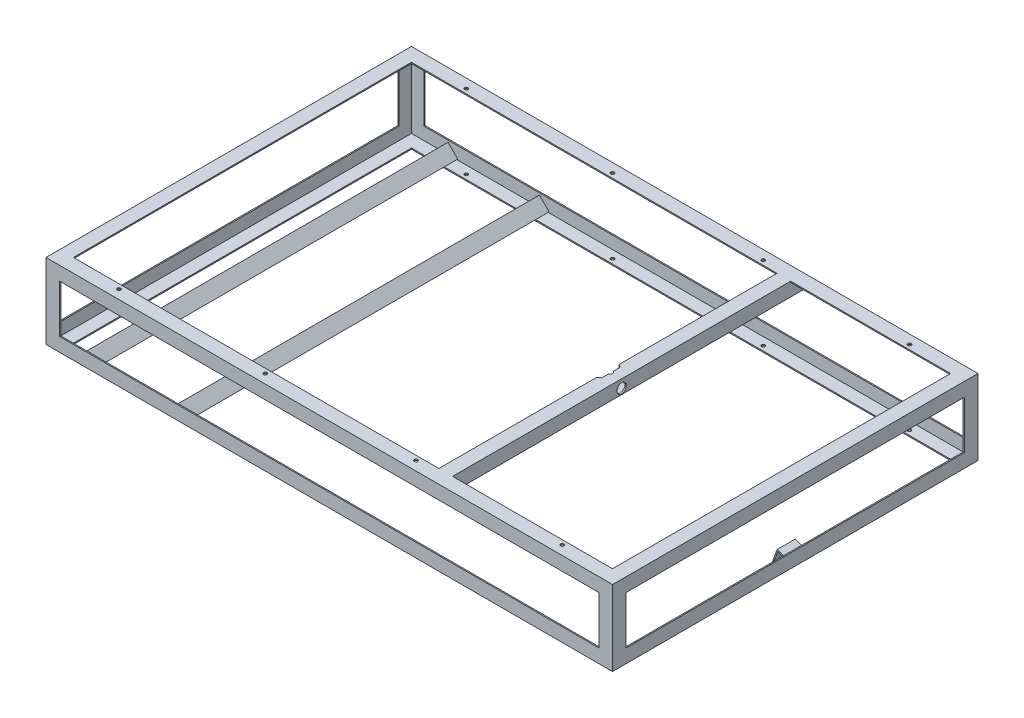
SolidWorks part; units mm, degrees
material "6061 Alloy"
ref_plane "Front Plane" through (0, 0, 0) normal (0, 0, 1) x (1, 0, 0)
ref_plane "Top Plane" through (0, 0, 0) normal (0, 1, 0) x (1, 0, 0)
ref_plane "Right Plane" through (0, 0, 0) normal (1, 0, 0) x (0, 0, -1)
other "Center of Mass"
sketch "Sketch2" plane through (0, 0, 0) normal (1, 0, 0) x (0, 0, -1)
  line L0 (-504.825, -346.075) -> (-504.825, -422.275)
  line L1 (504.825, -422.275) -> (-504.825, -422.275) construction
  line L2 (504.825, -422.275) -> (504.825, 422.275) construction
  line L3 (504.825, 422.275) -> (-504.825, 422.275) construction
  line L4 (-504.825, -422.275) -> (-504.825, 422.275) construction
  line L5 (504.825, -422.275) -> (-504.825, 422.275) construction
  line L6 (504.825, 422.275) -> (-504.825, -422.275) construction
  line L7 (-504.825, -422.275) -> (-428.625, -422.275)
  line L8 (-428.625, -422.275) -> (-428.625, -417.195)
  line L9 (-428.625, -417.195) -> (-498.7519, -417.195)
  line L10 (-498.7519, -417.195) -> (-498.7519, -346.075)
  line L11 (-498.7519, -346.075) -> (-504.825, -346.075)
  line L12 (0, 0) -> (0, -148.4726) construction
  line L13 (0, 0) -> (158.633, 0) construction
  line L14 (498.7519, -417.195) -> (498.7519, -346.075)
  line L15 (428.625, -417.195) -> (498.7519, -417.195)
  line L16 (428.625, -422.275) -> (428.625, -417.195)
  line L17 (504.825, -422.275) -> (428.625, -422.275)
  line L18 (504.825, -346.075) -> (504.825, -422.275)
  line L19 (498.7519, -346.075) -> (504.825, -346.075)
  line L20 (428.625, 417.195) -> (498.7519, 417.195)
  line L21 (428.625, 422.275) -> (428.625, 417.195)
  line L22 (504.825, 422.275) -> (428.625, 422.275)
  line L23 (504.825, 346.075) -> (504.825, 422.275)
  line L24 (498.7519, 346.075) -> (504.825, 346.075)
  line L25 (498.7519, 417.195) -> (498.7519, 346.075)
  line L26 (-498.7519, 417.195) -> (-498.7519, 346.075)
  line L27 (-428.625, 417.195) -> (-498.7519, 417.195)
  line L28 (-428.625, 422.275) -> (-428.625, 417.195)
  line L29 (-504.825, 422.275) -> (-428.625, 422.275)
  line L30 (-504.825, 346.075) -> (-504.825, 422.275)
  line L31 (-498.7519, 346.075) -> (-504.825, 346.075)
  point P0 (0, 0)
  dimension "D1" = 1009.65
  dimension "D2" = 844.55
  dimension "D3" = 76.2
  dimension "D4" = 5.08
extrude "OAL Lenth" [suppressed] add sketch "Sketch2" along normal blind 1574.8
sketch "Sketch3" [suppressed] plane through (0, 0, 0) normal (0, 0, 1) x (1, 0, 0)
  line L0 (0, -422.275) -> (0, -346.075)
  line L1 (1574.8, -346.075) -> (0, -346.075) construction
  line L2 (0, -346.075) -> (0, -422.275) construction
  line L3 (0, -346.075) -> (5.08, -346.075)
  line L4 (5.08, -346.075) -> (5.08, -417.195)
  line L5 (5.08, -417.195) -> (76.2, -417.195)
  line L6 (76.2, -417.195) -> (76.2, -422.275)
  line L7 (1574.8, -422.275) -> (0, -422.275) construction
  line L8 (76.2, -422.275) -> (0, -422.275)
  line L9 (0, 0) -> (697.1877, 0) construction
  line L10 (787.4, 346.075) -> (787.4, -346.075) construction
  line L11 (1574.8, 346.075) -> (0, 346.075) construction
  line L12 (76.2, 422.275) -> (0, 422.275)
  line L13 (76.2, 417.195) -> (76.2, 422.275)
  line L14 (5.08, 417.195) -> (76.2, 417.195)
  line L15 (5.08, 346.075) -> (5.08, 417.195)
  line L16 (0, 346.075) -> (5.08, 346.075)
  line L17 (0, 422.275) -> (0, 346.075)
  line L18 (1574.8, 422.275) -> (1574.8, 346.075)
  line L19 (1574.8, 346.075) -> (1569.72, 346.075)
  line L20 (1569.72, 346.075) -> (1569.72, 417.195)
  line L21 (1569.72, 417.195) -> (1498.6, 417.195)
  line L22 (1498.6, 417.195) -> (1498.6, 422.275)
  line L23 (1498.6, 422.275) -> (1574.8, 422.275)
  line L24 (1498.6, -422.275) -> (1574.8, -422.275)
  line L25 (1498.6, -417.195) -> (1498.6, -422.275)
  line L26 (1569.72, -417.195) -> (1498.6, -417.195)
  line L27 (1569.72, -346.075) -> (1569.72, -417.195)
  line L28 (1574.8, -346.075) -> (1569.72, -346.075)
  line L29 (1574.8, -422.275) -> (1574.8, -346.075)
  dimension "D1" = 5.08
extrude "OAL Width" [suppressed] add sketch "Sketch3" along normal up to surface and the other way up to surface
sketch "Sketch4" [suppressed] plane through (0, 422.275, 0) normal (0, 1, 0) x (1, 0, 0)
  line L0 (0, 504.825) -> (0, 428.625)
  line L1 (0, -428.625) -> (0, -504.825) construction
  line L2 (0, 428.625) -> (5.08, 428.625)
  line L3 (5.08, 428.625) -> (5.08, 499.745)
  line L4 (5.08, 499.745) -> (76.2, 499.745)
  line L5 (76.2, 499.745) -> (76.2, 504.825)
  line L6 (0, 504.825) -> (1574.8, 504.825) construction
  line L7 (76.2, 504.825) -> (0, 504.825)
  line L8 (0, 0) -> (1574.8, 0) construction
  line L9 (1574.8, -428.625) -> (1574.8, -504.825) construction
  line L10 (787.4, 0) -> (787.4, 504.825) construction
  line L11 (76.2, -504.825) -> (0, -504.825)
  line L12 (76.2, -499.745) -> (76.2, -504.825)
  line L13 (5.08, -499.745) -> (76.2, -499.745)
  line L14 (5.08, -428.625) -> (5.08, -499.745)
  line L15 (0, -428.625) -> (5.08, -428.625)
  line L16 (0, -504.825) -> (0, -428.625)
  line L17 (1574.8, -504.825) -> (1574.8, -428.625)
  line L18 (1574.8, -428.625) -> (1569.72, -428.625)
  line L19 (1569.72, -428.625) -> (1569.72, -499.745)
  line L20 (1569.72, -499.745) -> (1498.6, -499.745)
  line L21 (1498.6, -499.745) -> (1498.6, -504.825)
  line L22 (1498.6, -504.825) -> (1574.8, -504.825)
  line L23 (1498.6, 504.825) -> (1574.8, 504.825)
  line L24 (1498.6, 499.745) -> (1498.6, 504.825)
  line L25 (1569.72, 499.745) -> (1498.6, 499.745)
  line L26 (1569.72, 428.625) -> (1569.72, 499.745)
  line L27 (1574.8, 428.625) -> (1569.72, 428.625)
  line L28 (1574.8, 504.825) -> (1574.8, 428.625)
  dimension "D1" = 5.08
  dimension "D2" = 76.2
extrude "OAL Height" [suppressed] add sketch "Sketch4" against normal through all
sketch "Sketch5" plane through (0, 0, 0) normal (1, 0, 0) x (0, 0, -1)
  line L0 (0, 304.8) -> (0, -304.8) construction
  line L1 (-508, -304.8) -> (508, -304.8) construction
  line L2 (-508, -304.8) -> (-508, -266.7)
  line L3 (-508, -304.8) -> (-469.9, -304.8)
  line L4 (-469.9, -304.8) -> (-469.9, -301.625)
  line L5 (-469.9, -301.625) -> (-504.825, -301.625)
  line L6 (-504.825, -301.625) -> (-504.825, -266.7)
  line L7 (-504.825, -266.7) -> (-508, -266.7)
  line L8 (504.825, -266.7) -> (508, -266.7)
  line L9 (504.825, -301.625) -> (504.825, -266.7)
  line L10 (469.9, -301.625) -> (504.825, -301.625)
  line L11 (469.9, -304.8) -> (469.9, -301.625)
  line L12 (508, -304.8) -> (469.9, -304.8)
  line L13 (508, -304.8) -> (508, -266.7)
  line L14 (0, -200.025) -> (-176.3903, -200.025) construction
  line L15 (-508, -95.25) -> (508, -95.25) construction
  line L16 (508, -95.25) -> (508, -133.35)
  line L17 (508, -95.25) -> (469.9, -95.25)
  line L18 (469.9, -95.25) -> (469.9, -98.425)
  line L19 (469.9, -98.425) -> (504.825, -98.425)
  line L20 (504.825, -98.425) -> (504.825, -133.35)
  line L21 (504.825, -133.35) -> (508, -133.35)
  line L22 (-504.825, -133.35) -> (-508, -133.35)
  line L23 (-504.825, -98.425) -> (-504.825, -133.35)
  line L24 (-469.9, -98.425) -> (-504.825, -98.425)
  line L25 (-469.9, -95.25) -> (-469.9, -98.425)
  line L26 (-508, -95.25) -> (-469.9, -95.25)
  line L27 (-508, -95.25) -> (-508, -133.35)
  point P4 (0, 0)
  point P8 (0, -304.8)
  point P32 (0, -95.25)
  dimension "D1" = 1016
  dimension "D2" = 609.6
  dimension "D3" = 38.1
  dimension "D4" = 3.175
  dimension "D5" = 104.775
extrude "Bottom Horizontal Angle" add sketch "Sketch5" along normal blind 1574.8 separate body
sketch "Sketch6" plane through (0, -304.8, 0) normal (0, -1, 0) x (1, 0, 0)
  line L0 (0, 0) -> (1574.8, 0) construction
  line L1 (1574.8, -508) -> (1574.8, 508) construction
  line L2 (1574.8, -508) -> (1536.7, -508)
  line L3 (1574.8, -508) -> (1574.8, -469.9)
  line L4 (1574.8, -469.9) -> (1571.625, -469.9)
  line L5 (1571.625, -469.9) -> (1571.625, -504.825)
  line L6 (1571.625, -504.825) -> (1536.7, -504.825)
  line L7 (1536.7, -504.825) -> (1536.7, -508)
  line L8 (1536.7, 504.825) -> (1536.7, 508)
  line L9 (1571.625, 504.825) -> (1536.7, 504.825)
  line L10 (1571.625, 469.9) -> (1571.625, 504.825)
  line L11 (1574.8, 469.9) -> (1571.625, 469.9)
  line L12 (1574.8, 508) -> (1574.8, 469.9)
  line L13 (1574.8, 508) -> (1536.7, 508)
  line L15 (787.4, 0) -> (787.4, 197.6325) construction
  line L16 (0, -508) -> (0, 508) construction
  line L17 (0, 508) -> (38.1, 508)
  line L18 (0, 508) -> (0, 469.9)
  line L19 (0, 469.9) -> (3.175, 469.9)
  line L20 (3.175, 469.9) -> (3.175, 504.825)
  line L21 (3.175, 504.825) -> (38.1, 504.825)
  line L22 (38.1, 504.825) -> (38.1, 508)
  line L23 (38.1, -504.825) -> (38.1, -508)
  line L24 (3.175, -504.825) -> (38.1, -504.825)
  line L25 (3.175, -469.9) -> (3.175, -504.825)
  line L26 (0, -469.9) -> (3.175, -469.9)
  line L27 (0, -508) -> (0, -469.9)
  line L28 (0, -508) -> (38.1, -508)
  point P3 (787.4, 0)
  point P6 (1574.8, 0)
  point P32 (0, 0)
  dimension "D1" = 38.1
  dimension "D2" = 3.175
  dimension "D3" = 1016
  dimension "D4" = 1574.8
extrude "Front Vertial Angle" add sketch "Sketch6" against normal blind 209.55
sketch "Sketch12" plane through (0, 0, 0) normal (-1, 0, 0) x (0, 0, 1)
  line L0 (0, -304.8) -> (0, 304.8) construction
  line L1 (0, -304.8) -> (-469.9, -304.8) construction
  line L2 (-279.4, 304.8) -> (279.4, 304.8) construction
  line L3 (279.4, 304.8) -> (508, -95.25)
  line L4 (508, -95.25) -> (322.1581, -95.25)
  line L5 (469.9, -95.25) -> (508, -95.25) construction
  line L6 (508, -95.25) -> (508, -304.8) construction
  point P9 (0, 304.8)
  dimension "D1" = 609.6
  dimension "D2" = 558.8
ref_plane "Plane2" through (0, -95.25, 508) normal (0, -0.8682, 0.4961) x (-1, 0, 0)
sketch "Sketch13" plane through (0, -95.25, 508) normal (0, -0.8682, 0.4961) x (-1, 0, 0)
  line L0 (0, 0) -> (0, 38.1)
  line L1 (0, 485.1743) -> (0, 0) construction
  line L2 (0, 38.1) -> (-3.175, 38.1)
  line L3 (-3.175, 38.1) -> (-3.175, 3.175)
  line L4 (-3.175, 3.175) -> (-38.1, 3.175)
  line L5 (-38.1, 3.175) -> (-38.1, 0)
  line L6 (-1574.8, 0) -> (0, 0) construction
  line L7 (-38.1, 0) -> (0, 0)
  line L8 (0, 0) -> (-558.8, 0) construction
  line L9 (-279.4, 0) -> (-279.4, -79.7814) construction
  line L10 (-520.7, 0) -> (-558.8, 0)
  line L11 (-520.7, 3.175) -> (-520.7, 0)
  line L12 (-555.625, 3.175) -> (-520.7, 3.175)
  line L13 (-555.625, 38.1) -> (-555.625, 3.175)
  line L14 (-558.8, 38.1) -> (-555.625, 38.1)
  line L15 (-558.8, 0) -> (-558.8, 38.1)
  line L16 (-1574.8, 0) -> (0, 0) construction
  dimension "D1" = 3.175
  dimension "D2" = 38.1
  dimension "D3" = 558.8
extrude "Rear Diagonal Angle" [suppressed] add sketch "Sketch13" against normal up to vertex
sketch "Sketch14" [suppressed] plane through (0, 0, 0) normal (0, 0, 1) x (1, 0, 0)
  line L1 (0, 304.8) -> (0, -95.25) construction
  line L2 (0, -95.25) -> (558.8, -95.25) construction
  line L3 (279.4, -95.25) -> (279.4, 65.0322) construction
  line L4 (553.72, 266.7) -> (558.8, 266.7)
  line L5 (558.8, 266.7) -> (558.8, 304.8)
  line L6 (558.8, 304.8) -> (520.7, 304.8)
  line L12 (520.7, 304.8) -> (520.7, 299.72)
  line L13 (520.7, 299.72) -> (553.72, 299.72)
  line L26 (5.08, 299.72) -> (5.08, 266.7)
  line L27 (38.1, 299.72) -> (5.08, 299.72)
  line L28 (38.1, 304.8) -> (38.1, 299.72)
  line L29 (0, 304.8) -> (38.1, 304.8)
  line L30 (0, 266.7) -> (0, 304.8)
  line L31 (5.08, 266.7) -> (0, 266.7)
  line L32 (553.72, 299.72) -> (553.72, 266.7)
  dimension "D1" = 38.1
  dimension "D2" = 5.08
extrude "Rear Top Angle" [suppressed] add sketch "Sketch14" along normal up to next
sketch "Sketch7" plane through (0, -304.8, 0) normal (0, -1, 0) x (1, 0, 0)
  line L0 (609.6, 0) -> (0, 0) construction
  line L1 (0, 504.825) -> (0, -504.825) construction
  line L2 (0, 504.825) -> (50.8, 504.825)
  line L3 (0, 504.825) -> (0, 454.025)
  line L4 (0, 454.025) -> (3.175, 454.025)
  line L5 (3.175, 454.025) -> (3.175, 501.65)
  line L6 (3.175, 501.65) -> (50.8, 501.65)
  line L7 (50.8, 501.65) -> (50.8, 504.825)
  line L8 (50.8, -501.65) -> (50.8, -504.825)
  line L9 (3.175, -501.65) -> (50.8, -501.65)
  line L10 (3.175, -454.025) -> (3.175, -501.65)
  line L11 (0, -454.025) -> (3.175, -454.025)
  line L12 (0, -504.825) -> (0, -454.025)
  line L13 (0, -504.825) -> (50.8, -504.825)
  point P3 (304.8, 0)
  point P6 (0, 0)
extrude "Rear Vertical Angle" [suppressed] add sketch "Sketch7" against normal blind 609.6
sketch "Sketch8" plane through (0, 0, 0) normal (-1, 0, 0) x (0, 0, 1)
  line L0 (0, -304.8) -> (0, 304.8) construction
  line L2 (279.4, 304.8) -> (279.4, 266.7)
  line L3 (279.4, 304.8) -> (241.3, 304.8)
  line L4 (241.3, 304.8) -> (241.3, 301.625)
  line L5 (241.3, 301.625) -> (276.225, 301.625)
  line L6 (276.225, 301.625) -> (276.225, 266.7)
  line L7 (276.225, 266.7) -> (279.4, 266.7)
  point P3 (0, 0)
  point P6 (0, 304.8)
  dimension "D1" = 38.1
extrude "Rear Top Horizontal Angle" [suppressed] add sketch "Sketch8" against normal up to surface (558.8 mm away)
sketch "Sketch15" plane through (0, 0, 508) normal (0, 0, 1) x (1, 0, 0)
  line L0 (0, -266.7) -> (0, -304.8)
  line L1 (0, -95.25) -> (1574.8, -95.25) construction
  line L2 (787.4, -95.25) -> (787.4, 43.9233) construction
  line L3 (1571.625, -266.7) -> (1574.8, -266.7)
  line L4 (1571.625, -301.625) -> (1571.625, -266.7)
  line L5 (1536.7, -301.625) -> (1571.625, -301.625)
  line L6 (1536.7, -304.8) -> (1536.7, -301.625)
  line L7 (0, -304.8) -> (38.1, -304.8)
  line L8 (38.1, -304.8) -> (38.1, -301.625)
  line L9 (38.1, -301.625) -> (3.175, -301.625)
  line L10 (3.175, -301.625) -> (3.175, -266.7)
  line L11 (3.175, -266.7) -> (0, -266.7)
  line L12 (1574.8, -304.8) -> (1536.7, -304.8)
  line L13 (1574.8, -266.7) -> (1574.8, -304.8)
  line L20 (787.4, -95.25) -> (787.4, -304.8) construction
  line L21 (1574.8, -304.8) -> (0, -304.8) construction
  line L24 (787.4, -200.025) -> (896.4031, -200.025) construction
  line L27 (1574.8, -133.35) -> (1574.8, -95.25)
  line L28 (1574.8, -95.25) -> (1536.7, -95.25)
  line L29 (1536.7, -95.25) -> (1536.7, -98.425)
  line L30 (1536.7, -98.425) -> (1571.625, -98.425)
  line L31 (1571.625, -98.425) -> (1571.625, -133.35)
  line L32 (1571.625, -133.35) -> (1574.8, -133.35)
  line L33 (18.8814, -200.025) -> (113.1502, -200.025) construction
  line L35 (3.175, -133.35) -> (0, -133.35)
  line L36 (3.175, -98.425) -> (3.175, -133.35)
  line L37 (38.1, -98.425) -> (3.175, -98.425)
  line L38 (38.1, -95.25) -> (38.1, -98.425)
  line L39 (0, -95.25) -> (38.1, -95.25)
  line L40 (0, -133.35) -> (0, -95.25)
  dimension "D1" = 38.1
  dimension "D2" = 3.175
extrude "Boss-Extrude9" add sketch "Sketch15" against normal up to surface (508 mm away)
mirror "Mirror3" about plane through (0, 0, 0) normal (0, 0, 1)
sketch "Top Center Angle Plane" [suppressed] plane through (0, 0, 508) normal (0, 0, 1) x (1, 0, 0)
  line L0 (558.8, 304.8) -> (1574.8, -95.25)
  line L1 (558.8, 304.8) -> (509.3836, 179.2981)
ref_plane "Top Front Diagonal Angle PLane" [suppressed] through (379.8876, -149.5807, 0) normal (0.9305, -0.3664, 0) x (0, 0, -1)
sketch "Sketch10" [suppressed] plane through (379.8876, -149.5807, 0) normal (0.9305, -0.3664, 0) x (0, 0, -1)
  line L0 (-279.4, 488.3354) -> (279.4, 488.3354) construction
  line L1 (279.4, 488.3354) -> (-279.4, 488.3354) construction
  line L8 (-276.225, 450.2354) -> (-279.4, 450.2354)
  line L9 (-276.225, 485.1604) -> (-276.225, 450.2354)
  line L10 (-241.3, 485.1604) -> (-276.225, 485.1604)
  line L11 (-241.3, 488.3354) -> (-241.3, 485.1604)
  line L12 (-279.4, 488.3354) -> (-241.3, 488.3354)
  line L13 (-279.4, 488.3354) -> (-279.4, 450.2354)
  line L14 (0, 488.3354) -> (0, 449.1208) construction
  line L15 (279.4, 488.3354) -> (279.4, 450.2354)
  line L16 (279.4, 488.3354) -> (241.3, 488.3354)
  line L17 (241.3, 488.3354) -> (241.3, 485.1604)
  line L18 (241.3, 485.1604) -> (276.225, 485.1604)
  line L19 (276.225, 485.1604) -> (276.225, 450.2354)
  line L20 (276.225, 450.2354) -> (279.4, 450.2354)
  point P4 (0, 119.046)
  point P8 (0, 488.3354)
  dimension "D1" = 279.4
  dimension "D2" = 38.1
  dimension "D5" = 3.175
extrude "Top Front Diagonal Angle" [suppressed] add sketch "Sketch10" along normal up to vertex
sketch "Sketch11" [suppressed] plane through (0, 0, -504.825) normal (0, 0, -1) x (-1, 0, 0)
  line L0 (0, -101.6) -> (-1574.8, -101.6) construction
  line L1 (-1574.8, 101.6) -> (-1574.8, -304.8) construction
  line L2 (-1574.8, 101.6) -> (-1524, 101.6)
  line L3 (-1574.8, 101.6) -> (-1574.8, 50.8)
  line L4 (-1574.8, 50.8) -> (-1571.625, 50.8)
  line L5 (-1571.625, 50.8) -> (-1571.625, 98.425)
  line L6 (-1571.625, 98.425) -> (-1524, 98.425)
  line L7 (-1524, 98.425) -> (-1524, 101.6)
  line L8 (-1524, -301.625) -> (-1524, -304.8)
  line L9 (-1571.625, -301.625) -> (-1524, -301.625)
  line L10 (-1571.625, -254) -> (-1571.625, -301.625)
  line L11 (-1574.8, -254) -> (-1571.625, -254)
  line L12 (-1574.8, -304.8) -> (-1574.8, -254)
  line L13 (-1574.8, -304.8) -> (-1524, -304.8)
  line L14 (0, -304.8) -> (-50.8, -304.8)
  line L15 (-50.8, -301.625) -> (-50.8, -304.8)
  line L16 (-3.175, -254) -> (-3.175, -301.625)
  line L17 (0, -254) -> (-3.175, -254)
  line L18 (0, -304.8) -> (0, -254)
  line L19 (-3.175, -301.625) -> (-50.8, -301.625)
  line L20 (0, 0) -> (-419.4352, 0) construction
  line L21 (-3.175, 301.625) -> (-50.8, 301.625)
  line L22 (0, 304.8) -> (0, 254)
  line L23 (0, 254) -> (-3.175, 254)
  line L24 (-3.175, 254) -> (-3.175, 301.625)
  line L25 (-50.8, 301.625) -> (-50.8, 304.8)
  line L26 (0, 304.8) -> (-50.8, 304.8)
  line L27 (-605.3402, 263.2815) -> (-644.7354, 295.3543)
  line L28 (-605.3402, 263.2815) -> (-573.2675, 302.6767)
  line L29 (-642.7308, 297.8165) -> (-644.7354, 295.3543)
  line L30 (-605.7978, 267.7483) -> (-642.7308, 297.8165)
  line L31 (-573.2675, 302.6767) -> (-575.7297, 304.6813)
  line L32 (-575.7297, 304.6813) -> (-605.7978, 267.7483)
  line L33 (-643.7056, 301.2489) -> (-575.4944, 308.3511) construction
  line L38 (-643.7056, 301.2489) -> (-643.3359, 297.6977) construction
  line L40 (-575.4944, 308.3511) -> (-575.1246, 304.8) construction
  line L42 (0, 304.8) -> (-609.6, 304.8) construction
  line L43 (-1574.8, 101.6) -> (-609.6, 304.8) construction
  line L44 (-643.3359, 297.6977) -> (-575.1246, 304.8) construction
  line L45 (-609.2302, 301.2489) -> (-606.0734, 270.9299) construction
  line L46 (-642.7977, 298.5481) -> (-575.6628, 303.9496) construction
  line L47 (-609.2302, 301.2489) -> (-605.7978, 267.7483) construction
  point P3 (-787.4, -101.6)
  point P6 (-1574.8, -101.6)
  point P47 (-609.6, 304.8)
  point P51 (-575.4944, 308.3511)
  dimension "D1" = 50.8
  dimension "D2" = 3.175
  dimension "D3" = 68.58
extrude "Top Center Angle" [suppressed] add sketch "Sketch11" against normal through all
sketch "Sketch16" plane through (0, 0, 504.825) normal (0, 0, -1) x (-1, 0, 0)
  line L0 (-385.7158, -299.0624) -> (-358.775, -272.1217)
  line L1 (-1536.7, -301.625) -> (-38.1, -301.625) construction
  line L2 (-358.775, -272.1217) -> (-331.8342, -299.0624)
  line L4 (-331.8342, -299.0624) -> (-334.0793, -301.3075)
  line L5 (-334.0793, -301.3075) -> (-358.775, -276.6118)
  line L6 (-358.775, -276.6118) -> (-383.4707, -301.3075)
  line L7 (-383.4707, -301.3075) -> (-385.7158, -299.0624)
  line L8 (-383.4707, -301.3075) -> (-334.0793, -301.3075) construction
  line L9 (-358.775, -272.1217) -> (-358.775, -276.6118) construction
  line L10 (-358.775, -276.6118) -> (-358.775, -301.3075) construction
  line L12 (-3.175, -98.425) -> (-3.175, -301.625) construction
  line L13 (-129.4707, -301.3075) -> (-131.7158, -299.0624)
  line L14 (-131.7158, -299.0624) -> (-104.775, -272.1217)
  line L15 (-104.775, -272.1217) -> (-77.8342, -299.0624)
  line L16 (-77.8342, -299.0624) -> (-80.0793, -301.3075)
  line L17 (-80.0793, -301.3075) -> (-104.775, -276.6118)
  line L18 (-104.775, -276.6118) -> (-129.4707, -301.3075)
  dimension "D1" = 38.1
  dimension "D2" = 3.175
  dimension "D3" = 355.6
  dimension "D5" = 0.3175
  dimension "D4" = 2
extrude "Boss-Extrude14" add sketch "Sketch16" along normal up to next
sketch "Wheel Reference" plane through (0, 0, 0) normal (0, 0, 1) x (1, 0, 0)
  line L0 (1409.7, -317.5) -> (1003.3, -317.5) construction
  line L1 (1003.3, -317.5) -> (584.2, -317.5) construction
  line L2 (584.2, -317.5) -> (177.8, -317.5) construction
  line L3 (1409.7, -317.5) -> (1574.8, -317.5) construction
  line L4 (1574.8, -317.5) -> (1574.8, -304.8) construction
  line L5 (1574.8, -133.35) -> (1574.8, -266.7) construction
  line L6 (1536.7, -304.8) -> (38.1, -304.8) construction
  circle A0 centre (1409.7, -317.5) radius 190.5
  circle A1 centre (1003.3, -317.5) radius 190.5
  circle A2 centre (584.2, -317.5) radius 190.5
  circle A3 centre (177.8, -317.5) radius 190.5
  point P8 (1409.7, -508)
  point P12 (1574.8, -304.8)
  point P15 (1600.2, -317.5)
  dimension "D1" = 381
  dimension "D2" = 406.4
  dimension "D3" = 419.1
  dimension "D4" = 12.7
  dimension "D5" = 165.1
  dimension "D6" = 25.4
  dimension "D7" = 203.2
sketch "Sketch18" plane through (0, 0, 0) normal (0, 1, 0) x (1, 0, 0)
  line L0 (1409.7, 0) -> (1409.7, 482.6) construction
  line L1 (1574.8, 508) -> (0, 508) construction
  line L2 (1003.3, 0) -> (1003.3, 482.6) construction
  line L3 (1003.3, 0) -> (584.2, 0) construction
  line L4 (1409.7, 0) -> (1003.3, 0) construction
  line L5 (584.2, 0) -> (584.2, 482.6) construction
  line L6 (584.2, 0) -> (177.8, 0) construction
  line L7 (177.8, 0) -> (177.8, 482.6) construction
  line L8 (-12.7, 0) -> (368.3, 0) construction
  line L9 (0, 508) -> (0, -508) construction
  line L10 (177.8, 482.6) -> (584.2, 482.6) construction
  line L11 (584.2, 482.6) -> (1003.3, 482.6) construction
  line L12 (1003.3, 482.6) -> (1409.7, 482.6) construction
  line L13 (1409.7, 0) -> (0, 0) construction
  line L14 (1003.3, -482.6) -> (1409.7, -482.6) construction
  line L15 (584.2, -482.6) -> (1003.3, -482.6) construction
  line L16 (177.8, -482.6) -> (584.2, -482.6) construction
  circle A0 centre (1409.7, 482.6) radius 4.7625
  circle A1 centre (1003.3, 482.6) radius 4.7625
  circle A2 centre (584.2, 482.6) radius 4.7625
  circle A3 centre (177.8, 482.6) radius 4.7625
  circle A4 centre (177.8, -482.6) radius 4.7625
  circle A5 centre (584.2, -482.6) radius 4.7625
  circle A6 centre (1003.3, -482.6) radius 4.7625
  circle A7 centre (1409.7, -482.6) radius 4.7625
  point P35 (0, 0)
  dimension "D2" = 9.525
  dimension "D1" = 25.4
extrude "Wheel Mount LOC" cut sketch "Sketch18" against normal through all both and the other way through all
sketch "Sketch21" plane through (0, 0, 0) normal (0, 0, 1) x (1, 0, 0)
  line L0 (1584.4473, -280.7513) -> (1551.6286, -268.8062)
  line L2 (1551.6286, -268.8062) -> (1539.6835, -301.625)
  line L3 (1536.7, -301.625) -> (38.1, -301.625) construction
  line L4 (1539.6835, -301.625) -> (1536.7, -300.5391)
  line L5 (1536.7, -300.5391) -> (1549.731, -264.7368)
  line L6 (1549.731, -264.7368) -> (1585.5333, -277.7678)
  line L8 (1585.5333, -277.7678) -> (1584.4473, -280.7513)
  line L10 (1571.625, -98.425) -> (1571.625, -301.625) construction
  line L11 (1571.625, -301.625) -> (3.175, -301.625) construction
  line L12 (1536.7, -300.5391) -> (1536.7, -301.625)
  line L13 (1571.625, -276.0843) -> (1571.625, -272.7056)
  line L14 (1539.6835, -301.625) -> (1536.7, -301.625)
  point P22 (1536.7, -301.625)
  dimension "D1" = 3.175
  dimension "D2" = 38.1
  dimension "D3" = 20
  dimension "D4" = 23.2991
extrude "Boss-Extrude18" add sketch "Sketch21" along normal blind 25.4 and the other way blind 25.4 contours L0 L13 L6 L5 L4 L2 | L14 L4 L12
sketch "Sketch22" plane through (1453.5316, -529.0423, 0) normal (-0.9397, 0.342, 0) x (0, 0, 1)
  line L0 (0, 281.268) -> (0, 262.7415) construction
  line L1 (-25.4, 281.268) -> (25.4, 281.268) construction
  circle A0 centre (0, 262.7415) radius 4.7625
  dimension "D1" = 9.525
extrude "Cut-Extrude2" cut sketch "Sketch22" against normal up to next
sketch "Sketch23" plane through (0, 0, 504.825) normal (0, 0, -1) x (-1, 0, 0)
  line L0 (-1574.8, -189.6926) -> (-1066.8, -189.6926) construction
  line L1 (-1574.8, -266.7) -> (-1574.8, -133.35) construction
  line L2 (-1066.8, -189.6926) -> (-1066.8, -95.25) construction
  line L3 (-38.1, -95.25) -> (-1536.7, -95.25) construction
  line L4 (-1092.2, -133.35) -> (-1092.2, -95.25)
  line L5 (-1092.2, -95.25) -> (-1054.1, -95.25)
  line L6 (-1054.1, -95.25) -> (-1054.1, -98.425)
  line L7 (-1054.1, -98.425) -> (-1089.025, -98.425)
  line L8 (-1089.025, -98.425) -> (-1089.025, -133.35)
  line L9 (-1089.025, -133.35) -> (-1092.2, -133.35)
  line L11 (-1066.8, -95.25) -> (-1142.7166, -122.8814) construction
  line L13 (0, -95.25) -> (-1574.8, -95.25) construction
  line L14 (-1117.2307, -113.6053) -> (-1108.5434, -137.4735) construction
  line L15 (-1108.5434, -137.4735) -> (-1096.071, -132.9339) construction
  line L16 (-1108.5434, -137.4735) -> (-984.4013, -92.2894) construction
  line M17 (-3.175, -98.425) -> (-1571.625, -98.425)
  line M22 (-1536.7, -133.35) -> (-38.1, -133.35)
  dimension "D1" = 508
  dimension "D2" = 38.1
  dimension "D3" = 3.175
  dimension "D4" = 20
  dimension "D5" = 25.4
  dimension "D6" = 482.6
extrude "Boss-Extrude19" add sketch "Sketch23" along normal up to next contours L8 L7 L6 L4 M17 M22 | L8 L7 L6 L5 L4 M17
sketch "Sketch24" plane through (0, 0, 0) normal (0, 0, 1) x (1, 0, 0)
  line L0 (1065.1678, -87.5003) -> (1052.1368, -123.3026)
  line L1 (1052.1368, -123.3026) -> (1087.9391, -136.3335)
  line L2 (1087.9391, -136.3335) -> (1089.025, -133.35) construction
  line L3 (1089.025, -133.35) -> (1056.2062, -121.4049)
  line L4 (1056.2062, -121.4049) -> (1068.1513, -88.5862)
  line L5 (1068.1513, -88.5862) -> (1065.1678, -87.5003)
  line L6 (38.1, -95.25) -> (1054.1, -95.25) construction
  line L7 (1065.7259, -95.25) -> (1062.3471, -95.25)
  line L8 (1574.8, -95.25) -> (0, -95.25) construction
  line L9 (1092.2, -133.35) -> (1087.9391, -136.3335)
  line L10 (1089.025, -133.35) -> (1092.2, -133.35)
  dimension "D1" = 38.1
  dimension "D2" = 3.175
  dimension "D3" = 70
extrude "Boss-Extrude21" add sketch "Sketch24" along normal blind 25.4 and the other way blind 25.4 contours L1 L2 L3 L4 L7 L0 | L2 L9 L10
sketch "Sketch25" plane through (1453.5316, -529.0423, 0) normal (-0.9397, 0.342, 0) x (0, 0, 1)
  line L0 (0, 262.7415) -> (4.7625, 262.7415) construction
  circle A0 centre (0, 262.7415) radius 12.8588
  circle A1 centre (0, 262.7415) radius 4.7625 construction
  dimension "D1" = 25.7175
extrude "Cut-Extrude3" cut sketch "Sketch25" along normal blind 717.042
sketch "Sketch26" plane through (83.4479, 229.2714, 0) normal (-0.342, -0.9397, 0) x (0.9397, -0.342, 0)
  line L0 (1030.8571, 25.4) -> (1020.3275, 32.7729)
  line L1 (1020.3275, 32.7729) -> (1020.3275, -32.7729)
  line L2 (1020.3275, 0) -> (1030.8571, 0)
  line L3 (1030.8571, -25.4) -> (1030.8571, 25.4) construction
  line L4 (1030.8571, -25.4) -> (1030.8571, 25.4)
  line L5 (1030.8571, 25.4) -> (1068.9571, 25.4) construction
  line L6 (1030.8571, -25.4) -> (1020.3275, -32.7729)
  line M7 (1030.8571, 25.4) -> (1030.8571, -25.4)
  dimension "D1" = 35
extrude "Cut-Extrude4" cut sketch "Sketch26" against normal through all contours L6 L2 L1 M7 | L1 L2 L0 M7
